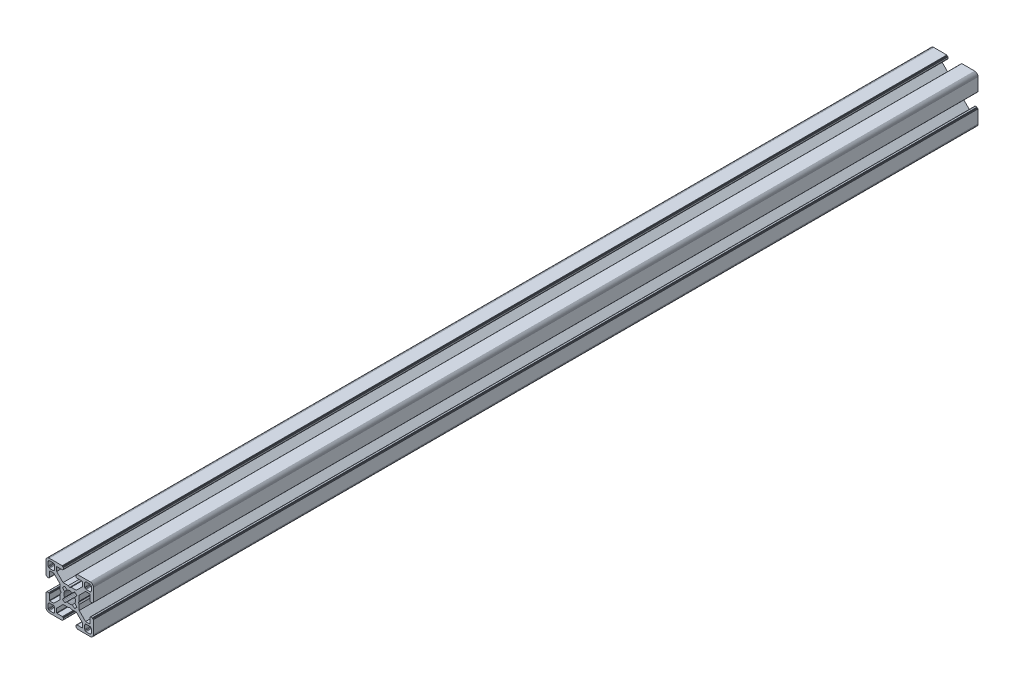
SolidWorks part; units mm, degrees
ref_plane "Front Plane" through (0, 0, 0) normal (0, 0, 1) x (1, 0, 0)
ref_plane "Top Plane" through (0, 0, 0) normal (0, 1, 0) x (1, 0, 0)
ref_plane "Right Plane" through (0, 0, 0) normal (1, 0, 0) x (0, 0, -1)
ref_plane "Plane1" through (0, 0, 0) normal (0, 0, 1) x (1, 0, 0)
sketch "Sketch1" plane through (0, 0, 0) normal (0, 0, 1) x (1, 0, 0)
  line L0 (28.3473, 29.9696) -> (28, 30)
  line L1 (28, 30) -> (19.75, 30)
  line L2 (19.75, 30) -> (19.7153, 29.997)
  line L3 (19.7153, 29.997) -> (19.6816, 29.9879)
  line L4 (19.6816, 29.9879) -> (19.65, 29.9732)
  line L5 (19.65, 29.9732) -> (19.6214, 29.9532)
  line L6 (19.6214, 29.9532) -> (19.5968, 29.9286)
  line L7 (19.5968, 29.9286) -> (19.5768, 29.9)
  line L8 (19.5768, 29.9) -> (19.5621, 29.8684)
  line L9 (19.5621, 29.8684) -> (19.553, 29.8347)
  line L10 (19.553, 29.8347) -> (19.55, 29.8)
  line L11 (19.55, 29.8) -> (19.55, 29.7)
  line L12 (19.55, 29.7) -> (19.547, 29.6653)
  line L13 (19.547, 29.6653) -> (19.5379, 29.6316)
  line L14 (19.5379, 29.6316) -> (19.5232, 29.6)
  line L15 (19.5232, 29.6) -> (19.5032, 29.5714)
  line L16 (19.5032, 29.5714) -> (19.4786, 29.5468)
  line L17 (19.4786, 29.5468) -> (19.45, 29.5268)
  line L18 (19.45, 29.5268) -> (19.4184, 29.5121)
  line L19 (19.4184, 29.5121) -> (19.3847, 29.503)
  line L20 (19.3847, 29.503) -> (19.35, 29.5)
  line L21 (19.35, 29.5) -> (19.25, 29.5)
  line L22 (19.25, 29.5) -> (19.2153, 29.497)
  line L23 (19.2153, 29.497) -> (19.1816, 29.4879)
  line L24 (19.1816, 29.4879) -> (19.15, 29.4732)
  line L25 (19.15, 29.4732) -> (19.1214, 29.4532)
  line L26 (19.1214, 29.4532) -> (19.0968, 29.4286)
  line L27 (19.0968, 29.4286) -> (19.0768, 29.4)
  line L28 (19.0768, 29.4) -> (19.0621, 29.3684)
  line L29 (19.0621, 29.3684) -> (19.053, 29.3347)
  line L30 (19.053, 29.3347) -> (19.05, 29.3)
  line L31 (19.05, 29.3) -> (19.05, 28.4)
  line L32 (19.05, 28.4) -> (19.0591, 28.2958)
  line L33 (19.0591, 28.2958) -> (19.0862, 28.1948)
  line L34 (19.0862, 28.1948) -> (19.1304, 28.1)
  line L35 (19.1304, 28.1) -> (19.1904, 28.0143)
  line L36 (19.1904, 28.0143) -> (19.2643, 27.9404)
  line L37 (19.2643, 27.9404) -> (19.35, 27.8804)
  line L38 (19.35, 27.8804) -> (19.4448, 27.8362)
  line L39 (19.4448, 27.8362) -> (19.5458, 27.8091)
  line L40 (19.5458, 27.8091) -> (19.65, 27.8)
  line L41 (19.65, 27.8) -> (23.05, 27.8)
  line L42 (23.05, 27.8) -> (23.0847, 27.7969)
  line L43 (23.0847, 27.7969) -> (23.1184, 27.7879)
  line L44 (23.1184, 27.7879) -> (23.15, 27.7732)
  line L45 (23.15, 27.7732) -> (23.1786, 27.7532)
  line L46 (23.1786, 27.7532) -> (23.2032, 27.7285)
  line L47 (23.2032, 27.7285) -> (23.2232, 27.7)
  line L48 (23.2232, 27.7) -> (23.2379, 27.6684)
  line L49 (23.2379, 27.6684) -> (23.247, 27.6347)
  line L50 (23.247, 27.6347) -> (23.25, 27.6)
  line L51 (23.25, 27.6) -> (23.25, 25.05)
  line L52 (23.25, 25.05) -> (19.2045, 21)
  line L53 (19.2045, 21) -> (15.9, 21)
  line L54 (15.9, 21) -> (15, 20.4848)
  line L55 (15, 20.4848) -> (14.1, 21)
  line L56 (14.1, 21) -> (10.7955, 21)
  line L57 (10.7955, 21) -> (7.9973, 23.8013)
  line L58 (7.9973, 23.8013) -> (6.75, 25.05)
  line L59 (6.75, 25.05) -> (6.75, 27.6)
  line L60 (6.75, 27.6) -> (6.753, 27.6347)
  line L61 (6.753, 27.6347) -> (6.7621, 27.6684)
  line L62 (6.7621, 27.6684) -> (6.7768, 27.7)
  line L63 (6.7768, 27.7) -> (6.7968, 27.7285)
  line L64 (6.7968, 27.7285) -> (6.8215, 27.7532)
  line L65 (6.8215, 27.7532) -> (6.85, 27.7732)
  line L66 (6.85, 27.7732) -> (6.8816, 27.7879)
  line L67 (6.8816, 27.7879) -> (6.9153, 27.7969)
  line L68 (6.9153, 27.7969) -> (6.95, 27.8)
  line L69 (6.95, 27.8) -> (10.35, 27.8)
  line L70 (10.35, 27.8) -> (10.4542, 27.8091)
  line L71 (10.4542, 27.8091) -> (10.5552, 27.8362)
  line L72 (10.5552, 27.8362) -> (10.65, 27.8804)
  line L73 (10.65, 27.8804) -> (10.7357, 27.9404)
  line L74 (10.7357, 27.9404) -> (10.8096, 28.0143)
  line L75 (10.8096, 28.0143) -> (10.8696, 28.1)
  line L76 (10.8696, 28.1) -> (10.9138, 28.1948)
  line L77 (10.9138, 28.1948) -> (10.9409, 28.2958)
  line L78 (10.9409, 28.2958) -> (10.95, 28.4)
  line L79 (10.95, 28.4) -> (10.95, 29.3)
  line L80 (10.95, 29.3) -> (10.947, 29.3347)
  line L81 (10.947, 29.3347) -> (10.938, 29.3684)
  line L82 (10.938, 29.3684) -> (10.9232, 29.4)
  line L83 (10.9232, 29.4) -> (10.9032, 29.4286)
  line L84 (10.9032, 29.4286) -> (10.8786, 29.4532)
  line L85 (10.8786, 29.4532) -> (10.85, 29.4732)
  line L86 (10.85, 29.4732) -> (10.8184, 29.4879)
  line L87 (10.8184, 29.4879) -> (10.7847, 29.497)
  line L88 (10.7847, 29.497) -> (10.75, 29.5)
  line L89 (10.75, 29.5) -> (10.65, 29.5)
  line L90 (10.65, 29.5) -> (10.6153, 29.503)
  line L91 (10.6153, 29.503) -> (10.5816, 29.5121)
  line L92 (10.5816, 29.5121) -> (10.55, 29.5268)
  line L93 (10.55, 29.5268) -> (10.5214, 29.5468)
  line L94 (10.5214, 29.5468) -> (10.4968, 29.5714)
  line L95 (10.4968, 29.5714) -> (10.4768, 29.6)
  line L96 (10.4768, 29.6) -> (10.4621, 29.6316)
  line L97 (10.4621, 29.6316) -> (10.453, 29.6653)
  line L98 (10.453, 29.6653) -> (10.45, 29.7)
  line L99 (10.45, 29.7) -> (10.45, 29.8)
  line L100 (10.45, 29.8) -> (10.447, 29.8347)
  line L101 (10.447, 29.8347) -> (10.4379, 29.8684)
  line L102 (10.4379, 29.8684) -> (10.4232, 29.9)
  line L103 (10.4232, 29.9) -> (10.4032, 29.9286)
  line L104 (10.4032, 29.9286) -> (10.3786, 29.9532)
  line L105 (10.3786, 29.9532) -> (10.35, 29.9732)
  line L106 (10.35, 29.9732) -> (10.3184, 29.9879)
  line L107 (10.3184, 29.9879) -> (10.2847, 29.997)
  line L108 (10.2847, 29.997) -> (10.25, 30)
  line L109 (10.25, 30) -> (2, 30)
  line L110 (2, 30) -> (1.6527, 29.9696)
  line L111 (1.6527, 29.9696) -> (1.316, 29.8794)
  line L112 (1.316, 29.8794) -> (1, 29.7321)
  line L113 (1, 29.7321) -> (0.7144, 29.5321)
  line L114 (0.7144, 29.5321) -> (0.4679, 29.2856)
  line L115 (0.4679, 29.2856) -> (0.2679, 29)
  line L116 (0.2679, 29) -> (0.1206, 28.684)
  line L117 (0.1206, 28.684) -> (0.0304, 28.3473)
  line L118 (0.0304, 28.3473) -> (0, 28)
  line L119 (0, 28) -> (0, 19.75)
  line L120 (0, 19.75) -> (0.003, 19.7153)
  line L121 (0.003, 19.7153) -> (0.0121, 19.6816)
  line L122 (0.0121, 19.6816) -> (0.0268, 19.65)
  line L123 (0.0268, 19.65) -> (0.0468, 19.6214)
  line L124 (0.0468, 19.6214) -> (0.0714, 19.5968)
  line L125 (0.0714, 19.5968) -> (0.1, 19.5768)
  line L126 (0.1, 19.5768) -> (0.1316, 19.5621)
  line L127 (0.1316, 19.5621) -> (0.1653, 19.553)
  line L128 (0.1653, 19.553) -> (0.2, 19.55)
  line L129 (0.2, 19.55) -> (0.3, 19.55)
  line L130 (0.3, 19.55) -> (0.3347, 19.547)
  line L131 (0.3347, 19.547) -> (0.3684, 19.5379)
  line L132 (0.3684, 19.5379) -> (0.4, 19.5232)
  line L133 (0.4, 19.5232) -> (0.4286, 19.5032)
  line L134 (0.4286, 19.5032) -> (0.4532, 19.4786)
  line L135 (0.4532, 19.4786) -> (0.4732, 19.45)
  line L136 (0.4732, 19.45) -> (0.4879, 19.4184)
  line L137 (0.4879, 19.4184) -> (0.497, 19.3847)
  line L138 (0.497, 19.3847) -> (0.5, 19.35)
  line L139 (0.5, 19.35) -> (0.5, 19.25)
  line L140 (0.5, 19.25) -> (0.503, 19.2153)
  line L141 (0.503, 19.2153) -> (0.5121, 19.1816)
  line L142 (0.5121, 19.1816) -> (0.5268, 19.15)
  line L143 (0.5268, 19.15) -> (0.5468, 19.1214)
  line L144 (0.5468, 19.1214) -> (0.5714, 19.0968)
  line L145 (0.5714, 19.0968) -> (0.6, 19.0768)
  line L146 (0.6, 19.0768) -> (0.6316, 19.0621)
  line L147 (0.6316, 19.0621) -> (0.6653, 19.053)
  line L148 (0.6653, 19.053) -> (0.7, 19.05)
  line L149 (0.7, 19.05) -> (1.6, 19.05)
  line L150 (1.6, 19.05) -> (1.7042, 19.0591)
  line L151 (1.7042, 19.0591) -> (1.8052, 19.0862)
  line L152 (1.8052, 19.0862) -> (1.9, 19.1304)
  line L153 (1.9, 19.1304) -> (1.9857, 19.1904)
  line L154 (1.9857, 19.1904) -> (2.0596, 19.2643)
  line L155 (2.0596, 19.2643) -> (2.1196, 19.35)
  line L156 (2.1196, 19.35) -> (2.1638, 19.4448)
  line L157 (2.1638, 19.4448) -> (2.1909, 19.5458)
  line L158 (2.1909, 19.5458) -> (2.2, 19.65)
  line L159 (2.2, 19.65) -> (2.2, 23.05)
  line L160 (2.2, 23.05) -> (2.203, 23.0847)
  line L161 (2.203, 23.0847) -> (2.2121, 23.1184)
  line L162 (2.2121, 23.1184) -> (2.2268, 23.15)
  line L163 (2.2268, 23.15) -> (2.2468, 23.1786)
  line L164 (2.2468, 23.1786) -> (2.2714, 23.2032)
  line L165 (2.2714, 23.2032) -> (2.3, 23.2232)
  line L166 (2.3, 23.2232) -> (2.3316, 23.2379)
  line L167 (2.3316, 23.2379) -> (2.3653, 23.247)
  line L168 (2.3653, 23.247) -> (2.4, 23.25)
  line L169 (2.4, 23.25) -> (4.95, 23.25)
  line L170 (4.95, 23.25) -> (7.9973, 20.2027)
  line L171 (7.9973, 20.2027) -> (8.9955, 19.2045)
  line L172 (8.9955, 19.2045) -> (8.9955, 15.9)
  line L173 (8.9955, 15.9) -> (9.5151, 15)
  line L174 (9.5151, 15) -> (8.9955, 14.1)
  line L175 (8.9955, 14.1) -> (8.9955, 10.7955)
  line L176 (8.9955, 10.7955) -> (4.95, 6.75)
  line L177 (4.95, 6.75) -> (2.4, 6.75)
  line L178 (2.4, 6.75) -> (2.3653, 6.753)
  line L179 (2.3653, 6.753) -> (2.3316, 6.7621)
  line L180 (2.3316, 6.7621) -> (2.3, 6.7768)
  line L181 (2.3, 6.7768) -> (2.2714, 6.7968)
  line L182 (2.2714, 6.7968) -> (2.2468, 6.8214)
  line L183 (2.2468, 6.8214) -> (2.2268, 6.85)
  line L184 (2.2268, 6.85) -> (2.2121, 6.8816)
  line L185 (2.2121, 6.8816) -> (2.203, 6.9153)
  line L186 (2.203, 6.9153) -> (2.2, 6.95)
  line L187 (2.2, 6.95) -> (2.2, 10.35)
  line L188 (2.2, 10.35) -> (2.1909, 10.4542)
  line L189 (2.1909, 10.4542) -> (2.1638, 10.5552)
  line L190 (2.1638, 10.5552) -> (2.1196, 10.65)
  line L191 (2.1196, 10.65) -> (2.0596, 10.7357)
  line L192 (2.0596, 10.7357) -> (1.9857, 10.8096)
  line L193 (1.9857, 10.8096) -> (1.9, 10.8696)
  line L194 (1.9, 10.8696) -> (1.8052, 10.9138)
  line L195 (1.8052, 10.9138) -> (1.7042, 10.9409)
  line L196 (1.7042, 10.9409) -> (1.6, 10.95)
  line L197 (1.6, 10.95) -> (0.7, 10.95)
  line L198 (0.7, 10.95) -> (0.6653, 10.9469)
  line L199 (0.6653, 10.9469) -> (0.6316, 10.9379)
  line L200 (0.6316, 10.9379) -> (0.6, 10.9232)
  line L201 (0.6, 10.9232) -> (0.5715, 10.9032)
  line L202 (0.5715, 10.9032) -> (0.5468, 10.8785)
  line L203 (0.5468, 10.8785) -> (0.5268, 10.85)
  line L204 (0.5268, 10.85) -> (0.5121, 10.8184)
  line L205 (0.5121, 10.8184) -> (0.503, 10.7847)
  line L206 (0.503, 10.7847) -> (0.5, 10.75)
  line L207 (0.5, 10.75) -> (0.5, 10.65)
  line L208 (0.5, 10.65) -> (0.497, 10.6153)
  line L209 (0.497, 10.6153) -> (0.4879, 10.5816)
  line L210 (0.4879, 10.5816) -> (0.4732, 10.55)
  line L211 (0.4732, 10.55) -> (0.4532, 10.5214)
  line L212 (0.4532, 10.5214) -> (0.4286, 10.4968)
  line L213 (0.4286, 10.4968) -> (0.4, 10.4768)
  line L214 (0.4, 10.4768) -> (0.3684, 10.4621)
  line L215 (0.3684, 10.4621) -> (0.3347, 10.453)
  line L216 (0.3347, 10.453) -> (0.3, 10.45)
  line L217 (0.3, 10.45) -> (0.2, 10.45)
  line L218 (0.2, 10.45) -> (0.1653, 10.447)
  line L219 (0.1653, 10.447) -> (0.1316, 10.4379)
  line L220 (0.1316, 10.4379) -> (0.1, 10.4232)
  line L221 (0.1, 10.4232) -> (0.0714, 10.4032)
  line L222 (0.0714, 10.4032) -> (0.0468, 10.3786)
  line L223 (0.0468, 10.3786) -> (0.0268, 10.35)
  line L224 (0.0268, 10.35) -> (0.0121, 10.3184)
  line L225 (0.0121, 10.3184) -> (0.003, 10.2847)
  line L226 (0.003, 10.2847) -> (0, 10.25)
  line L227 (0, 10.25) -> (0, 2)
  line L228 (0, 2) -> (0.0304, 1.6527)
  line L229 (0.0304, 1.6527) -> (0.1206, 1.316)
  line L230 (0.1206, 1.316) -> (0.2679, 1)
  line L231 (0.2679, 1) -> (0.4679, 0.7144)
  line L232 (0.4679, 0.7144) -> (0.7144, 0.4679)
  line L233 (0.7144, 0.4679) -> (1, 0.2679)
  line L234 (1, 0.2679) -> (1.316, 0.1206)
  line L235 (1.316, 0.1206) -> (1.6527, 0.0304)
  line L236 (1.6527, 0.0304) -> (2, 0)
  line L237 (2, 0) -> (10.25, 0)
  line L238 (10.25, 0) -> (10.2847, 0.003)
  line L239 (10.2847, 0.003) -> (10.3184, 0.0121)
  line L240 (10.3184, 0.0121) -> (10.35, 0.0268)
  line L241 (10.35, 0.0268) -> (10.3786, 0.0468)
  line L242 (10.3786, 0.0468) -> (10.4032, 0.0714)
  line L243 (10.4032, 0.0714) -> (10.4232, 0.1)
  line L244 (10.4232, 0.1) -> (10.4379, 0.1316)
  line L245 (10.4379, 0.1316) -> (10.447, 0.1653)
  line L246 (10.447, 0.1653) -> (10.45, 0.2)
  line L247 (10.45, 0.2) -> (10.45, 0.3)
  line L248 (10.45, 0.3) -> (10.453, 0.3347)
  line L249 (10.453, 0.3347) -> (10.4621, 0.3684)
  line L250 (10.4621, 0.3684) -> (10.4768, 0.4)
  line L251 (10.4768, 0.4) -> (10.4968, 0.4286)
  line L252 (10.4968, 0.4286) -> (10.5214, 0.4532)
  line L253 (10.5214, 0.4532) -> (10.55, 0.4732)
  line L254 (10.55, 0.4732) -> (10.5816, 0.4879)
  line L255 (10.5816, 0.4879) -> (10.6153, 0.497)
  line L256 (10.6153, 0.497) -> (10.65, 0.5)
  line L257 (10.65, 0.5) -> (10.75, 0.5)
  line L258 (10.75, 0.5) -> (10.7847, 0.503)
  line L259 (10.7847, 0.503) -> (10.8184, 0.5121)
  line L260 (10.8184, 0.5121) -> (10.85, 0.5268)
  line L261 (10.85, 0.5268) -> (10.8785, 0.5468)
  line L262 (10.8785, 0.5468) -> (10.9032, 0.5715)
  line L263 (10.9032, 0.5715) -> (10.9232, 0.6)
  line L264 (10.9232, 0.6) -> (10.9379, 0.6316)
  line L265 (10.9379, 0.6316) -> (10.9469, 0.6653)
  line L266 (10.9469, 0.6653) -> (10.95, 0.7)
  line L267 (10.95, 0.7) -> (10.95, 1.6)
  line L268 (10.95, 1.6) -> (10.9409, 1.7042)
  line L269 (10.9409, 1.7042) -> (10.9138, 1.8052)
  line L270 (10.9138, 1.8052) -> (10.8696, 1.9)
  line L271 (10.8696, 1.9) -> (10.8096, 1.9857)
  line L272 (10.8096, 1.9857) -> (10.7357, 2.0596)
  line L273 (10.7357, 2.0596) -> (10.65, 2.1196)
  line L274 (10.65, 2.1196) -> (10.5552, 2.1638)
  line L275 (10.5552, 2.1638) -> (10.4542, 2.1909)
  line L276 (10.4542, 2.1909) -> (10.35, 2.2)
  line L277 (10.35, 2.2) -> (6.95, 2.2)
  line L278 (6.95, 2.2) -> (6.9153, 2.203)
  line L279 (6.9153, 2.203) -> (6.8816, 2.212)
  line L280 (6.8816, 2.212) -> (6.85, 2.2268)
  line L281 (6.85, 2.2268) -> (6.8215, 2.2468)
  line L282 (6.8215, 2.2468) -> (6.7968, 2.2714)
  line L283 (6.7968, 2.2714) -> (6.7768, 2.3)
  line L284 (6.7768, 2.3) -> (6.7621, 2.3316)
  line L285 (6.7621, 2.3316) -> (6.753, 2.3653)
  line L286 (6.753, 2.3653) -> (6.75, 2.4)
  line L287 (6.75, 2.4) -> (6.75, 4.95)
  line L288 (6.75, 4.95) -> (9.7875, 7.9908)
  line L289 (9.7875, 7.9908) -> (10.7955, 9)
  line L290 (10.7955, 9) -> (14.1, 9)
  line L291 (14.1, 9) -> (15, 9.5151)
  line L292 (15, 9.5151) -> (15.9, 9)
  line L293 (15.9, 9) -> (19.2045, 9)
  line L294 (19.2045, 9) -> (20.2126, 7.9908)
  line L295 (20.2126, 7.9908) -> (23.25, 4.95)
  line L296 (23.25, 4.95) -> (23.25, 2.4)
  line L297 (23.25, 2.4) -> (23.247, 2.3653)
  line L298 (23.247, 2.3653) -> (23.2379, 2.3316)
  line L299 (23.2379, 2.3316) -> (23.2232, 2.3)
  line L300 (23.2232, 2.3) -> (23.2032, 2.2714)
  line L301 (23.2032, 2.2714) -> (23.1786, 2.2468)
  line L302 (23.1786, 2.2468) -> (23.15, 2.2268)
  line L303 (23.15, 2.2268) -> (23.1184, 2.212)
  line L304 (23.1184, 2.212) -> (23.0847, 2.203)
  line L305 (23.0847, 2.203) -> (23.05, 2.2)
  line L306 (23.05, 2.2) -> (19.65, 2.2)
  line L307 (19.65, 2.2) -> (19.5458, 2.1909)
  line L308 (19.5458, 2.1909) -> (19.4448, 2.1638)
  line L309 (19.4448, 2.1638) -> (19.35, 2.1196)
  line L310 (19.35, 2.1196) -> (19.2643, 2.0596)
  line L311 (19.2643, 2.0596) -> (19.1904, 1.9857)
  line L312 (19.1904, 1.9857) -> (19.1304, 1.9)
  line L313 (19.1304, 1.9) -> (19.0862, 1.8052)
  line L314 (19.0862, 1.8052) -> (19.0591, 1.7042)
  line L315 (19.0591, 1.7042) -> (19.05, 1.6)
  line L316 (19.05, 1.6) -> (19.05, 0.7)
  line L317 (19.05, 0.7) -> (19.053, 0.6653)
  line L318 (19.053, 0.6653) -> (19.0621, 0.6316)
  line L319 (19.0621, 0.6316) -> (19.0768, 0.6)
  line L320 (19.0768, 0.6) -> (19.0968, 0.5714)
  line L321 (19.0968, 0.5714) -> (19.1214, 0.5468)
  line L322 (19.1214, 0.5468) -> (19.15, 0.5268)
  line L323 (19.15, 0.5268) -> (19.1816, 0.5121)
  line L324 (19.1816, 0.5121) -> (19.2153, 0.503)
  line L325 (19.2153, 0.503) -> (19.25, 0.5)
  line L326 (19.25, 0.5) -> (19.35, 0.5)
  line L327 (19.35, 0.5) -> (19.3847, 0.497)
  line L328 (19.3847, 0.497) -> (19.4184, 0.4879)
  line L329 (19.4184, 0.4879) -> (19.45, 0.4732)
  line L330 (19.45, 0.4732) -> (19.4786, 0.4532)
  line L331 (19.4786, 0.4532) -> (19.5032, 0.4286)
  line L332 (19.5032, 0.4286) -> (19.5232, 0.4)
  line L333 (19.5232, 0.4) -> (19.5379, 0.3684)
  line L334 (19.5379, 0.3684) -> (19.547, 0.3347)
  line L335 (19.547, 0.3347) -> (19.55, 0.3)
  line L336 (19.55, 0.3) -> (19.55, 0.2)
  line L337 (19.55, 0.2) -> (19.553, 0.1653)
  line L338 (19.553, 0.1653) -> (19.5621, 0.1316)
  line L339 (19.5621, 0.1316) -> (19.5768, 0.1)
  line L340 (19.5768, 0.1) -> (19.5968, 0.0714)
  line L341 (19.5968, 0.0714) -> (19.6214, 0.0468)
  line L342 (19.6214, 0.0468) -> (19.65, 0.0268)
  line L343 (19.65, 0.0268) -> (19.6816, 0.0121)
  line L344 (19.6816, 0.0121) -> (19.7153, 0.003)
  line L345 (19.7153, 0.003) -> (19.75, 0)
  line L346 (19.75, 0) -> (28, 0)
  line L347 (28, 0) -> (28.3473, 0.0304)
  line L348 (28.3473, 0.0304) -> (28.684, 0.1206)
  line L349 (28.684, 0.1206) -> (29, 0.2679)
  line L350 (29, 0.2679) -> (29.2856, 0.4679)
  line L351 (29.2856, 0.4679) -> (29.5321, 0.7144)
  line L352 (29.5321, 0.7144) -> (29.7321, 1)
  line L353 (29.7321, 1) -> (29.8794, 1.316)
  line L354 (29.8794, 1.316) -> (29.9696, 1.6527)
  line L355 (29.9696, 1.6527) -> (30, 2)
  line L356 (30, 2) -> (30, 10.25)
  line L357 (30, 10.25) -> (29.997, 10.2847)
  line L358 (29.997, 10.2847) -> (29.988, 10.3184)
  line L359 (29.988, 10.3184) -> (29.9732, 10.35)
  line L360 (29.9732, 10.35) -> (29.9532, 10.3785)
  line L361 (29.9532, 10.3785) -> (29.9286, 10.4032)
  line L362 (29.9286, 10.4032) -> (29.9, 10.4232)
  line L363 (29.9, 10.4232) -> (29.8684, 10.4379)
  line L364 (29.8684, 10.4379) -> (29.8347, 10.447)
  line L365 (29.8347, 10.447) -> (29.8, 10.45)
  line L366 (29.8, 10.45) -> (29.7, 10.45)
  line L367 (29.7, 10.45) -> (29.6649, 10.4534)
  line L368 (29.6649, 10.4534) -> (29.6312, 10.4624)
  line L369 (29.6312, 10.4624) -> (29.5996, 10.4772)
  line L370 (29.5996, 10.4772) -> (29.5711, 10.4972)
  line L371 (29.5711, 10.4972) -> (29.5464, 10.5218)
  line L372 (29.5464, 10.5218) -> (29.5264, 10.5504)
  line L373 (29.5264, 10.5504) -> (29.5117, 10.582)
  line L374 (29.5117, 10.582) -> (29.5027, 10.6156)
  line L375 (29.5027, 10.6156) -> (29.4996, 10.6504)
  line L376 (29.4996, 10.6504) -> (29.4996, 10.7504)
  line L377 (29.4996, 10.7504) -> (29.497, 10.7847)
  line L378 (29.497, 10.7847) -> (29.4879, 10.8184)
  line L379 (29.4879, 10.8184) -> (29.4732, 10.85)
  line L380 (29.4732, 10.85) -> (29.4532, 10.8785)
  line L381 (29.4532, 10.8785) -> (29.4286, 10.9032)
  line L382 (29.4286, 10.9032) -> (29.4, 10.9232)
  line L383 (29.4, 10.9232) -> (29.3684, 10.9379)
  line L384 (29.3684, 10.9379) -> (29.3347, 10.9469)
  line L385 (29.3347, 10.9469) -> (29.3, 10.95)
  line L386 (29.3, 10.95) -> (28.4, 10.95)
  line L387 (28.4, 10.95) -> (28.2958, 10.9409)
  line L388 (28.2958, 10.9409) -> (28.1948, 10.9138)
  line L389 (28.1948, 10.9138) -> (28.1, 10.8696)
  line L390 (28.1, 10.8696) -> (28.0143, 10.8096)
  line L391 (28.0143, 10.8096) -> (27.9404, 10.7357)
  line L392 (27.9404, 10.7357) -> (27.8804, 10.65)
  line L393 (27.8804, 10.65) -> (27.8362, 10.5552)
  line L394 (27.8362, 10.5552) -> (27.8091, 10.4542)
  line L395 (27.8091, 10.4542) -> (27.8, 10.35)
  line L396 (27.8, 10.35) -> (27.8, 6.95)
  line L397 (27.8, 6.95) -> (27.797, 6.9153)
  line L398 (27.797, 6.9153) -> (27.7879, 6.8816)
  line L399 (27.7879, 6.8816) -> (27.7732, 6.85)
  line L400 (27.7732, 6.85) -> (27.7532, 6.8214)
  line L401 (27.7532, 6.8214) -> (27.7286, 6.7968)
  line L402 (27.7286, 6.7968) -> (27.7, 6.7768)
  line L403 (27.7, 6.7768) -> (27.6684, 6.7621)
  line L404 (27.6684, 6.7621) -> (27.6347, 6.753)
  line L405 (27.6347, 6.753) -> (27.6, 6.75)
  line L406 (27.6, 6.75) -> (25.05, 6.75)
  line L407 (25.05, 6.75) -> (23.8092, 7.9908)
  line L408 (23.8092, 7.9908) -> (21.0045, 10.7955)
  line L409 (21.0045, 10.7955) -> (21.0045, 14.1)
  line L410 (21.0045, 14.1) -> (20.4849, 15)
  line L411 (20.4849, 15) -> (21.0045, 15.9)
  line L412 (21.0045, 15.9) -> (21.0045, 19.2045)
  line L413 (21.0045, 19.2045) -> (25.05, 23.25)
  line L414 (25.05, 23.25) -> (27.6, 23.25)
  line L415 (27.6, 23.25) -> (27.6347, 23.247)
  line L416 (27.6347, 23.247) -> (27.6684, 23.2379)
  line L417 (27.6684, 23.2379) -> (27.7, 23.2232)
  line L418 (27.7, 23.2232) -> (27.7286, 23.2032)
  line L419 (27.7286, 23.2032) -> (27.7532, 23.1786)
  line L420 (27.7532, 23.1786) -> (27.7732, 23.15)
  line L421 (27.7732, 23.15) -> (27.7879, 23.1184)
  line L422 (27.7879, 23.1184) -> (27.797, 23.0847)
  line L423 (27.797, 23.0847) -> (27.8, 23.05)
  line L424 (27.8, 23.05) -> (27.8, 19.65)
  line L425 (27.8, 19.65) -> (27.8091, 19.5458)
  line L426 (27.8091, 19.5458) -> (27.8362, 19.4448)
  line L427 (27.8362, 19.4448) -> (27.8804, 19.35)
  line L428 (27.8804, 19.35) -> (27.9404, 19.2643)
  line L429 (27.9404, 19.2643) -> (28.0143, 19.1904)
  line L430 (28.0143, 19.1904) -> (28.1, 19.1304)
  line L431 (28.1, 19.1304) -> (28.1948, 19.0862)
  line L432 (28.1948, 19.0862) -> (28.2958, 19.0591)
  line L433 (28.2958, 19.0591) -> (28.4, 19.05)
  line L434 (28.4, 19.05) -> (29.3, 19.05)
  line L435 (29.3, 19.05) -> (29.3347, 19.053)
  line L436 (29.3347, 19.053) -> (29.3684, 19.0621)
  line L437 (29.3684, 19.0621) -> (29.4, 19.0768)
  line L438 (29.4, 19.0768) -> (29.4282, 19.0971)
  line L439 (29.4282, 19.0971) -> (29.4528, 19.1218)
  line L440 (29.4528, 19.1218) -> (29.4728, 19.1504)
  line L441 (29.4728, 19.1504) -> (29.4876, 19.182)
  line L442 (29.4876, 19.182) -> (29.4966, 19.2156)
  line L443 (29.4966, 19.2156) -> (29.4996, 19.2504)
  line L444 (29.4996, 19.2504) -> (29.4996, 19.3504)
  line L445 (29.4996, 19.3504) -> (29.5027, 19.3851)
  line L446 (29.5027, 19.3851) -> (29.5117, 19.4188)
  line L447 (29.5117, 19.4188) -> (29.5264, 19.4504)
  line L448 (29.5264, 19.4504) -> (29.5464, 19.4789)
  line L449 (29.5464, 19.4789) -> (29.5711, 19.5036)
  line L450 (29.5711, 19.5036) -> (29.5996, 19.5236)
  line L451 (29.5996, 19.5236) -> (29.6312, 19.5383)
  line L452 (29.6312, 19.5383) -> (29.6649, 19.5473)
  line L453 (29.6649, 19.5473) -> (29.7, 19.55)
  line L454 (29.7, 19.55) -> (29.8, 19.55)
  line L455 (29.8, 19.55) -> (29.8347, 19.553)
  line L456 (29.8347, 19.553) -> (29.8684, 19.5621)
  line L457 (29.8684, 19.5621) -> (29.9, 19.5768)
  line L458 (29.9, 19.5768) -> (29.9286, 19.5968)
  line L459 (29.9286, 19.5968) -> (29.9532, 19.6214)
  line L460 (29.9532, 19.6214) -> (29.9732, 19.65)
  line L461 (29.9732, 19.65) -> (29.9879, 19.6816)
  line L462 (29.9879, 19.6816) -> (29.997, 19.7153)
  line L463 (29.997, 19.7153) -> (30, 19.75)
  line L464 (30, 19.75) -> (30, 28)
  line L465 (30, 28) -> (29.9696, 28.3473)
  line L466 (29.9696, 28.3473) -> (29.8794, 28.684)
  line L467 (29.8794, 28.684) -> (29.7321, 29)
  line L468 (29.7321, 29) -> (29.5321, 29.2856)
  line L469 (29.5321, 29.2856) -> (29.2856, 29.5321)
  line L470 (29.2856, 29.5321) -> (29, 29.7321)
  line L471 (29, 29.7321) -> (28.684, 29.8794)
  line L472 (28.684, 29.8794) -> (28.3473, 29.9696)
  line L473 (1.3, 25.5) -> (1.3, 27.7)
  line L474 (1.3, 27.7) -> (1.3123, 27.8564)
  line L475 (1.3123, 27.8564) -> (1.3489, 28.009)
  line L476 (1.3489, 28.009) -> (1.409, 28.154)
  line L477 (1.409, 28.154) -> (1.491, 28.2878)
  line L478 (1.491, 28.2878) -> (1.5929, 28.4071)
  line L479 (1.5929, 28.4071) -> (1.7122, 28.509)
  line L480 (1.7122, 28.509) -> (1.846, 28.591)
  line L481 (1.846, 28.591) -> (1.991, 28.6511)
  line L482 (1.991, 28.6511) -> (2.1436, 28.6877)
  line L483 (2.1436, 28.6877) -> (2.3, 28.7)
  line L484 (2.3, 28.7) -> (4.5, 28.7)
  line L485 (4.5, 28.7) -> (4.6564, 28.6877)
  line L486 (4.6564, 28.6877) -> (4.809, 28.6511)
  line L487 (4.809, 28.6511) -> (4.954, 28.591)
  line L488 (4.954, 28.591) -> (5.0878, 28.509)
  line L489 (5.0878, 28.509) -> (5.2071, 28.4071)
  line L490 (5.2071, 28.4071) -> (5.309, 28.2878)
  line L491 (5.309, 28.2878) -> (5.391, 28.154)
  line L492 (5.391, 28.154) -> (5.4511, 28.009)
  line L493 (5.4511, 28.009) -> (5.4877, 27.8564)
  line L494 (5.4877, 27.8564) -> (5.5, 27.7)
  line L495 (5.5, 27.7) -> (5.5, 25.5)
  line L496 (5.5, 25.5) -> (5.4877, 25.3436)
  line L497 (5.4877, 25.3436) -> (5.4511, 25.191)
  line L498 (5.4511, 25.191) -> (5.391, 25.046)
  line L499 (5.391, 25.046) -> (5.309, 24.9122)
  line L500 (5.309, 24.9122) -> (5.2071, 24.7929)
  line L501 (5.2071, 24.7929) -> (5.0878, 24.691)
  line L502 (5.0878, 24.691) -> (4.954, 24.609)
  line L503 (4.954, 24.609) -> (4.809, 24.5489)
  line L504 (4.809, 24.5489) -> (4.6564, 24.5123)
  line L505 (4.6564, 24.5123) -> (4.5, 24.5)
  line L506 (4.5, 24.5) -> (2.3, 24.5)
  line L507 (2.3, 24.5) -> (2.1436, 24.5123)
  line L508 (2.1436, 24.5123) -> (1.991, 24.5489)
  line L509 (1.991, 24.5489) -> (1.846, 24.609)
  line L510 (1.846, 24.609) -> (1.7122, 24.691)
  line L511 (1.7122, 24.691) -> (1.5929, 24.7929)
  line L512 (1.5929, 24.7929) -> (1.491, 24.9122)
  line L513 (1.491, 24.9122) -> (1.409, 25.046)
  line L514 (1.409, 25.046) -> (1.3489, 25.191)
  line L515 (1.3489, 25.191) -> (1.3123, 25.3436)
  line L516 (1.3123, 25.3436) -> (1.3, 25.5)
  line L517 (25.3436, 28.6877) -> (25.5, 28.7)
  line L518 (25.5, 28.7) -> (27.7, 28.7)
  line L519 (27.7, 28.7) -> (27.8564, 28.6877)
  line L520 (27.8564, 28.6877) -> (28.009, 28.6511)
  line L521 (28.009, 28.6511) -> (28.154, 28.591)
  line L522 (28.154, 28.591) -> (28.2878, 28.509)
  line L523 (28.2878, 28.509) -> (28.4071, 28.4071)
  line L524 (28.4071, 28.4071) -> (28.509, 28.2878)
  line L525 (28.509, 28.2878) -> (28.591, 28.154)
  line L526 (28.591, 28.154) -> (28.6511, 28.009)
  line L527 (28.6511, 28.009) -> (28.6877, 27.8564)
  line L528 (28.6877, 27.8564) -> (28.7, 27.7)
  line L529 (28.7, 27.7) -> (28.7, 25.5)
  line L530 (28.7, 25.5) -> (28.6877, 25.3436)
  line L531 (28.6877, 25.3436) -> (28.6511, 25.191)
  line L532 (28.6511, 25.191) -> (28.591, 25.046)
  line L533 (28.591, 25.046) -> (28.509, 24.9122)
  line L534 (28.509, 24.9122) -> (28.4071, 24.7929)
  line L535 (28.4071, 24.7929) -> (28.2878, 24.691)
  line L536 (28.2878, 24.691) -> (28.154, 24.609)
  line L537 (28.154, 24.609) -> (28.009, 24.5489)
  line L538 (28.009, 24.5489) -> (27.8564, 24.5123)
  line L539 (27.8564, 24.5123) -> (27.7, 24.5)
  line L540 (27.7, 24.5) -> (25.5, 24.5)
  line L541 (25.5, 24.5) -> (25.3436, 24.5123)
  line L542 (25.3436, 24.5123) -> (25.191, 24.5489)
  line L543 (25.191, 24.5489) -> (25.046, 24.609)
  line L544 (25.046, 24.609) -> (24.9122, 24.691)
  line L545 (24.9122, 24.691) -> (24.7929, 24.7929)
  line L546 (24.7929, 24.7929) -> (24.691, 24.9122)
  line L547 (24.691, 24.9122) -> (24.609, 25.046)
  line L548 (24.609, 25.046) -> (24.5489, 25.191)
  line L549 (24.5489, 25.191) -> (24.5123, 25.3436)
  line L550 (24.5123, 25.3436) -> (24.5, 25.5)
  line L551 (24.5, 25.5) -> (24.5, 27.7)
  line L552 (24.5, 27.7) -> (24.5123, 27.8564)
  line L553 (24.5123, 27.8564) -> (24.5489, 28.009)
  line L554 (24.5489, 28.009) -> (24.609, 28.154)
  line L555 (24.609, 28.154) -> (24.691, 28.2878)
  line L556 (24.691, 28.2878) -> (24.7929, 28.4071)
  line L557 (24.7929, 28.4071) -> (24.9122, 28.509)
  line L558 (24.9122, 28.509) -> (25.046, 28.591)
  line L559 (25.046, 28.591) -> (25.191, 28.6511)
  line L560 (25.191, 28.6511) -> (25.3436, 28.6877)
  line L561 (15, 18.65) -> (15.55, 18.6083)
  line L562 (15.55, 18.6083) -> (16.0875, 18.4842)
  line L563 (16.0875, 18.4842) -> (16.6001, 18.2806)
  line L564 (16.6001, 18.2806) -> (18.1359, 19.5184)
  line L565 (18.1359, 19.5184) -> (18.645, 19.1187)
  line L566 (18.645, 19.1187) -> (19.1036, 18.6621)
  line L567 (19.1036, 18.6621) -> (19.5053, 18.1547)
  line L568 (19.5053, 18.1547) -> (18.2806, 16.6001)
  line L569 (18.2806, 16.6001) -> (18.4842, 16.0875)
  line L570 (18.4842, 16.0875) -> (18.6083, 15.55)
  line L571 (18.6083, 15.55) -> (18.65, 15)
  line L572 (18.65, 15) -> (18.6083, 14.45)
  line L573 (18.6083, 14.45) -> (18.4842, 13.9125)
  line L574 (18.4842, 13.9125) -> (18.2806, 13.3999)
  line L575 (18.2806, 13.3999) -> (19.5053, 11.8453)
  line L576 (19.5053, 11.8453) -> (19.1036, 11.3379)
  line L577 (19.1036, 11.3379) -> (18.645, 10.8813)
  line L578 (18.645, 10.8813) -> (18.1359, 10.4816)
  line L579 (18.1359, 10.4816) -> (16.6001, 11.7194)
  line L580 (16.6001, 11.7194) -> (16.0875, 11.5158)
  line L581 (16.0875, 11.5158) -> (15.55, 11.3917)
  line L582 (15.55, 11.3917) -> (15, 11.35)
  line L583 (15, 11.35) -> (14.45, 11.3917)
  line L584 (14.45, 11.3917) -> (13.9125, 11.5158)
  line L585 (13.9125, 11.5158) -> (13.3999, 11.7194)
  line L586 (13.3999, 11.7194) -> (11.8641, 10.4816)
  line L587 (11.8641, 10.4816) -> (11.355, 10.8813)
  line L588 (11.355, 10.8813) -> (10.8964, 11.3379)
  line L589 (10.8964, 11.3379) -> (10.4947, 11.8453)
  line L590 (10.4947, 11.8453) -> (11.7194, 13.3999)
  line L591 (11.7194, 13.3999) -> (11.5158, 13.9125)
  line L592 (11.5158, 13.9125) -> (11.3917, 14.45)
  line L593 (11.3917, 14.45) -> (11.35, 15)
  line L594 (11.35, 15) -> (11.3917, 15.55)
  line L595 (11.3917, 15.55) -> (11.5158, 16.0875)
  line L596 (11.5158, 16.0875) -> (11.7194, 16.6001)
  line L597 (11.7194, 16.6001) -> (10.4947, 18.1547)
  line L598 (10.4947, 18.1547) -> (10.8964, 18.6621)
  line L599 (10.8964, 18.6621) -> (11.355, 19.1187)
  line L600 (11.355, 19.1187) -> (11.8641, 19.5184)
  line L601 (11.8641, 19.5184) -> (13.3999, 18.2806)
  line L602 (13.3999, 18.2806) -> (13.9125, 18.4842)
  line L603 (13.9125, 18.4842) -> (14.45, 18.6083)
  line L604 (14.45, 18.6083) -> (15, 18.65)
  line L605 (4.5, 1.3) -> (2.3, 1.3)
  line L606 (2.3, 1.3) -> (2.1436, 1.3123)
  line L607 (2.1436, 1.3123) -> (1.991, 1.3489)
  line L608 (1.991, 1.3489) -> (1.846, 1.409)
  line L609 (1.846, 1.409) -> (1.7122, 1.491)
  line L610 (1.7122, 1.491) -> (1.5929, 1.5929)
  line L611 (1.5929, 1.5929) -> (1.491, 1.7122)
  line L612 (1.491, 1.7122) -> (1.409, 1.846)
  line L613 (1.409, 1.846) -> (1.3489, 1.991)
  line L614 (1.3489, 1.991) -> (1.3123, 2.1436)
  line L615 (1.3123, 2.1436) -> (1.3, 2.3)
  line L616 (1.3, 2.3) -> (1.3, 4.5)
  line L617 (1.3, 4.5) -> (1.3123, 4.6564)
  line L618 (1.3123, 4.6564) -> (1.3489, 4.809)
  line L619 (1.3489, 4.809) -> (1.409, 4.954)
  line L620 (1.409, 4.954) -> (1.491, 5.0878)
  line L621 (1.491, 5.0878) -> (1.5929, 5.2071)
  line L622 (1.5929, 5.2071) -> (1.7122, 5.309)
  line L623 (1.7122, 5.309) -> (1.846, 5.391)
  line L624 (1.846, 5.391) -> (1.991, 5.4511)
  line L625 (1.991, 5.4511) -> (2.1436, 5.4877)
  line L626 (2.1436, 5.4877) -> (2.3, 5.5)
  line L627 (2.3, 5.5) -> (4.5, 5.5)
  line L628 (4.5, 5.5) -> (4.6564, 5.4877)
  line L629 (4.6564, 5.4877) -> (4.809, 5.4511)
  line L630 (4.809, 5.4511) -> (4.954, 5.391)
  line L631 (4.954, 5.391) -> (5.0878, 5.309)
  line L632 (5.0878, 5.309) -> (5.2071, 5.2071)
  line L633 (5.2071, 5.2071) -> (5.309, 5.0878)
  line L634 (5.309, 5.0878) -> (5.391, 4.954)
  line L635 (5.391, 4.954) -> (5.4511, 4.809)
  line L636 (5.4511, 4.809) -> (5.4877, 4.6564)
  line L637 (5.4877, 4.6564) -> (5.5, 4.5)
  line L638 (5.5, 4.5) -> (5.5, 2.3)
  line L639 (5.5, 2.3) -> (5.4877, 2.1436)
  line L640 (5.4877, 2.1436) -> (5.4511, 1.991)
  line L641 (5.4511, 1.991) -> (5.391, 1.846)
  line L642 (5.391, 1.846) -> (5.309, 1.7122)
  line L643 (5.309, 1.7122) -> (5.2071, 1.5929)
  line L644 (5.2071, 1.5929) -> (5.0878, 1.491)
  line L645 (5.0878, 1.491) -> (4.954, 1.409)
  line L646 (4.954, 1.409) -> (4.809, 1.3489)
  line L647 (4.809, 1.3489) -> (4.6564, 1.3123)
  line L648 (4.6564, 1.3123) -> (4.5, 1.3)
  line L649 (27.7, 1.3) -> (25.5, 1.3)
  line L650 (25.5, 1.3) -> (25.3436, 1.3123)
  line L651 (25.3436, 1.3123) -> (25.191, 1.3489)
  line L652 (25.191, 1.3489) -> (25.046, 1.409)
  line L653 (25.046, 1.409) -> (24.9122, 1.491)
  line L654 (24.9122, 1.491) -> (24.7929, 1.5929)
  line L655 (24.7929, 1.5929) -> (24.691, 1.7122)
  line L656 (24.691, 1.7122) -> (24.609, 1.846)
  line L657 (24.609, 1.846) -> (24.5489, 1.991)
  line L658 (24.5489, 1.991) -> (24.5123, 2.1436)
  line L659 (24.5123, 2.1436) -> (24.5, 2.3)
  line L660 (24.5, 2.3) -> (24.5, 4.5)
  line L661 (24.5, 4.5) -> (24.5123, 4.6564)
  line L662 (24.5123, 4.6564) -> (24.5489, 4.809)
  line L663 (24.5489, 4.809) -> (24.609, 4.954)
  line L664 (24.609, 4.954) -> (24.691, 5.0878)
  line L665 (24.691, 5.0878) -> (24.7929, 5.2071)
  line L666 (24.7929, 5.2071) -> (24.9122, 5.309)
  line L667 (24.9122, 5.309) -> (25.046, 5.391)
  line L668 (25.046, 5.391) -> (25.191, 5.4511)
  line L669 (25.191, 5.4511) -> (25.3436, 5.4877)
  line L670 (25.3436, 5.4877) -> (25.5, 5.5)
  line L671 (25.5, 5.5) -> (27.7, 5.5)
  line L672 (27.7, 5.5) -> (27.8564, 5.4877)
  line L673 (27.8564, 5.4877) -> (28.009, 5.4511)
  line L674 (28.009, 5.4511) -> (28.154, 5.391)
  line L675 (28.154, 5.391) -> (28.2878, 5.309)
  line L676 (28.2878, 5.309) -> (28.4071, 5.2071)
  line L677 (28.4071, 5.2071) -> (28.509, 5.0878)
  line L678 (28.509, 5.0878) -> (28.591, 4.954)
  line L679 (28.591, 4.954) -> (28.6511, 4.809)
  line L680 (28.6511, 4.809) -> (28.6877, 4.6564)
  line L681 (28.6877, 4.6564) -> (28.7, 4.5)
  line L682 (28.7, 4.5) -> (28.7, 2.3)
  line L683 (28.7, 2.3) -> (28.6877, 2.1436)
  line L684 (28.6877, 2.1436) -> (28.6511, 1.991)
  line L685 (28.6511, 1.991) -> (28.591, 1.846)
  line L686 (28.591, 1.846) -> (28.509, 1.7122)
  line L687 (28.509, 1.7122) -> (28.4071, 1.5929)
  line L688 (28.4071, 1.5929) -> (28.2878, 1.491)
  line L689 (28.2878, 1.491) -> (28.154, 1.409)
  line L690 (28.154, 1.409) -> (28.009, 1.3489)
  line L691 (28.009, 1.3489) -> (27.8564, 1.3123)
  line L692 (27.8564, 1.3123) -> (27.7, 1.3)
extrude "Boss-Extrude1" add sketch "Sketch1" against normal blind 560
